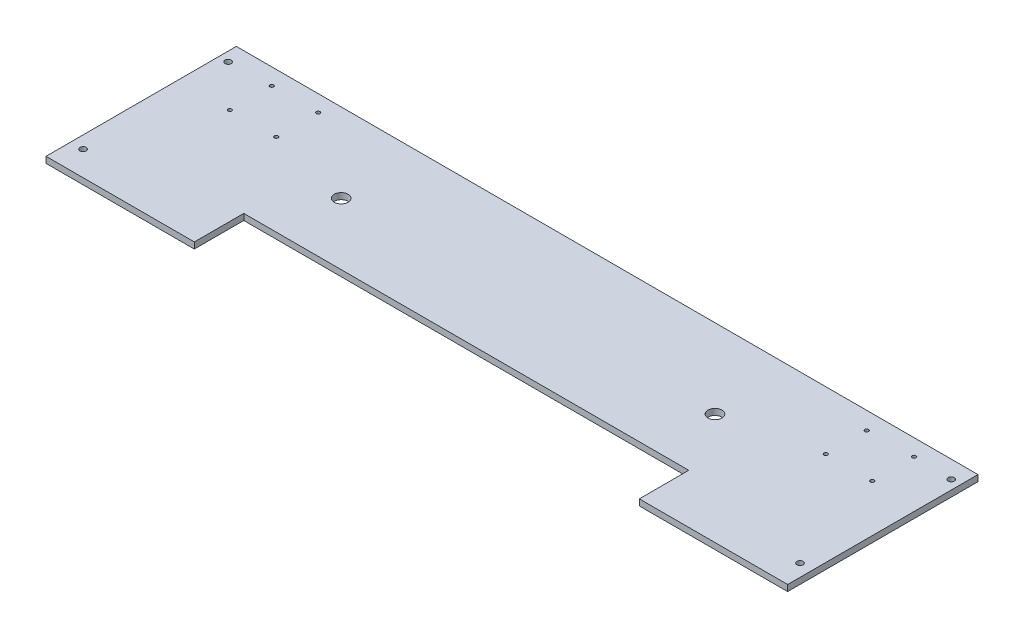
SolidWorks part; units mm, degrees
ref_plane "Front Plane" through (0, 0, 0) normal (0, 0, 1) x (1, 0, 0)
ref_plane "Top Plane" through (0, 0, 0) normal (0, 1, 0) x (1, 0, 0)
ref_plane "Right Plane" through (0, 0, 0) normal (1, 0, 0) x (0, 0, -1)
sketch "Sketch1" plane through (0, 0, 0) normal (0, 1, 0) x (1, 0, 0)
  line L0 (0, 0) -> (457.2, 0)
  line L1 (457.2, 0) -> (457.2, -50.8)
  line L2 (457.2, -50.8) -> (609.6, -50.8)
  line L3 (609.6, -50.8) -> (609.6, 144.78)
  line L4 (609.6, 144.78) -> (-152.4, 144.78)
  line L5 (0, 0) -> (0, -50.8)
  line L6 (0, -50.8) -> (-152.4, -50.8)
  line L7 (-152.4, -50.8) -> (-152.4, 144.78)
  dimension "D1" = 195.58
  dimension "D2" = 195.58
  dimension "D3" = 457.2
  dimension "D4" = 762
  dimension "D5" = 152.4
  dimension "D6" = 152.4
  dimension "D7" = 144.78
extrude "Boss-Extrude1" add sketch "Sketch1" along normal blind 6.35 contours L4 L7 L6 L5 L0 L1 L2 L3
sketch "Sketch3" plane through (0, 6.35, 0) normal (0, 1, 0) x (1, 0, 0)
  line L0 (-152.4, -50.8) -> (-152.4, 144.78) construction
  line L1 (0, -50.8) -> (-152.4, -50.8) construction
  line L2 (609.6, 144.78) -> (-152.4, 144.78) construction
  line L3 (609.6, 144.78) -> (-152.4, 144.78) construction
  line L4 (-152.4, -50.8) -> (-152.4, 144.78) construction
  line L5 (0, 0) -> (457.2, 0) construction
  line L8 (609.6, -50.8) -> (609.6, 144.78) construction
  line L9 (457.2, -50.8) -> (609.6, -50.8) construction
  circle A0 centre (-139.7, -25.4) radius 3.175
  circle A1 centre (-99.1108, 84.8106) radius 1.905
  circle A2 centre (-142.875, 126.8171) radius 3.175
  circle A3 centre (-51.435, 84.8106) radius 1.905
  circle A4 centre (-51.435, 127.8636) radius 1.905
  circle A5 centre (36.576, 63.5) radius 7.1438
  circle A6 centre (600.075, 126.8171) radius 3.175
  circle A7 centre (596.9, -25.4) radius 3.175
  circle A8 centre (560.959, 127.8636) radius 1.905
  circle A9 centre (513.207, 84.8106) radius 1.905
  circle A10 centre (560.959, 84.8106) radius 1.905
  circle A11 centre (513.207, 126.8171) radius 1.905
  circle A12 centre (420.624, 63.5) radius 7.1438
  circle A13 centre (-99.1108, 127.8636) radius 1.905
  dimension "D1" = 6.35
  dimension "D2" = 12.7
  dimension "D3" = 25.4
  dimension "D4" = 3.81
  dimension "D5" = 53.2892
  dimension "D6" = 59.9694
  dimension "D7" = 6.35
  dimension "D8" = 9.525
  dimension "D9" = 17.9629
  dimension "D10" = 3.81
  dimension "D11" = 59.9694
  dimension "D12" = 100.965
  dimension "D13" = 3.81
  dimension "D14" = 100.965
  dimension "D15" = 16.9164
  dimension "D16" = 14.2875
  dimension "D17" = 188.976
  dimension "D18" = 63.5
  dimension "D20" = 6.35
  dimension "D21" = 9.525
  dimension "D22" = 17.9629
  dimension "D23" = 6.35
  dimension "D24" = 12.7
  dimension "D25" = 25.4
  dimension "D26" = 3.81
  dimension "D27" = 48.641
  dimension "D28" = 16.9164
  dimension "D29" = 3.81
  dimension "D30" = 59.9694
  dimension "D31" = 96.393
  dimension "D32" = 3.81
  dimension "D33" = 48.641
  dimension "D34" = 59.9694
  dimension "D35" = 3.81
  dimension "D36" = 17.9629
  dimension "D37" = 96.393
  dimension "D38" = 14.2875
  dimension "D39" = 81.28
  dimension "D40" = 188.976
  dimension "D19" = 3.81
  dimension "D41" = 16.9164
  dimension "D42" = 53.2892
extrude "Cut-Extrude1" cut sketch "Sketch3" against normal blind 7.62
sketch "Sketch5" plane through (0, 6.35, 0) normal (0, 1, 0) x (1, 0, 0)
  line L0 (609.6, 144.78) -> (-152.4, 144.78) construction
  line L1 (44.45, 144.78) -> (412.75, 144.78)
  line L2 (44.45, 144.78) -> (44.45, 0)
  line L3 (44.45, 0) -> (412.75, 0)
  line L4 (412.75, 144.78) -> (412.75, 0)
  line L5 (0, 0) -> (457.2, 0) construction
  line L7 (457.2, 0) -> (457.2, -50.8) construction
  line L8 (-152.4, -50.8) -> (-152.4, 144.78) construction
  line L9 (0, 0) -> (0, -50.8) construction
  circle A1 centre (36.576, 63.5) radius 7.1438 construction
  circle A3 centre (420.624, 63.5) radius 7.1438 construction
  circle A4 centre (50.8, 12.7) radius 3.175
  circle A5 centre (57.15, 91.44) radius 3.175
  circle A6 centre (169.6134, 119.38) radius 3.175
  point P10 (457.2, -25.4)
  dimension "D5" = 7.874
  dimension "D7" = 44.45
  dimension "D1" = 7.874
  dimension "D9" = 6.35
  dimension "D10" = 6.35
  dimension "D11" = 12.7
  dimension "D12" = 6.35
  dimension "D13" = 6.35
  dimension "D14" = 53.34
  dimension "D15" = 12.7
  dimension "D16" = 25.4
  dimension "D2" = 7.874
  dimension "D3" = 196.85
  dimension "D4" = 7.874
  dimension "D6" = 368.3
  dimension "D8" = 144.78
